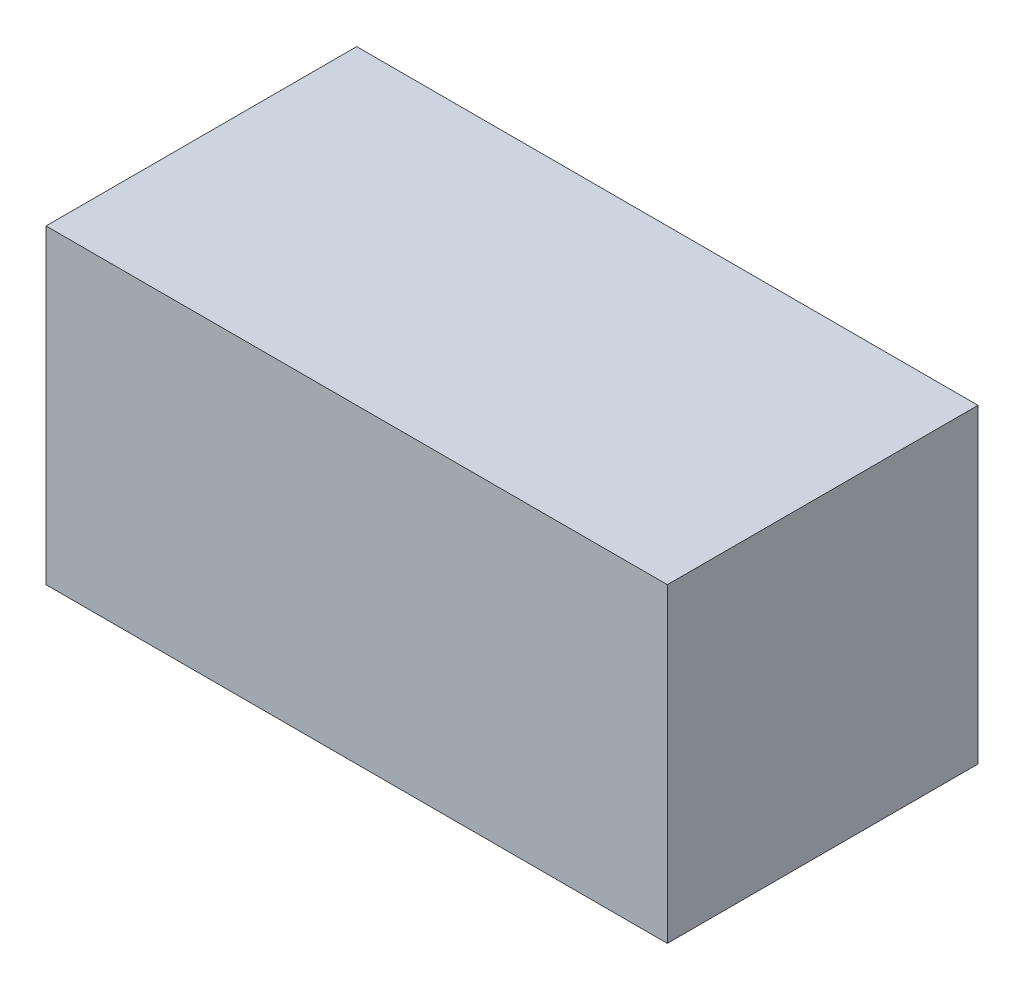
SolidWorks part; units mm, degrees
material "6061-T6 (SS)"
ref_plane "Front Plane" through (0, 0, 0) normal (0, 0, 1) x (1, 0, 0)
ref_plane "Top Plane" through (0, 0, 0) normal (0, 1, 0) x (1, 0, 0)
ref_plane "Right Plane" through (0, 0, 0) normal (1, 0, 0) x (0, 0, -1)
sketch "Sketch1" plane through (0, 0, 0) normal (0, 1, 0) x (1, 0, 0)
  line L1 (-250, -125) -> (250, -125)
  line L2 (-250, -125) -> (-250, 125)
  line L3 (-250, 125) -> (250, 125)
  line L4 (250, -125) -> (250, 125)
  line L5 (-250, -125) -> (250, 125) construction
  line L6 (-250, 125) -> (250, -125) construction
  point P0 (0, 0)
  dimension "D1" = 500
  dimension "D2" = 250
extrude "Boss-Extrude1" add sketch "Sketch1" along normal blind 250
